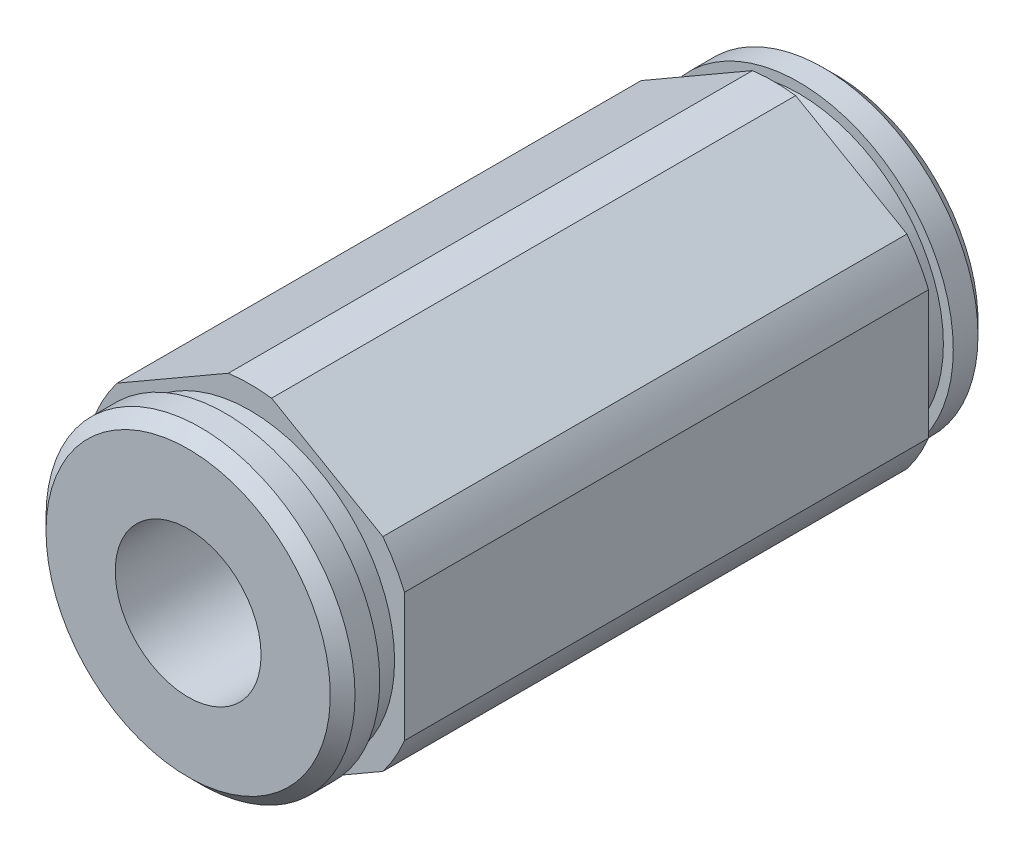
SolidWorks part; units mm, degrees
material "ThunderHex"
ref_plane "Front Plane" through (0, 0, 0) normal (0, 0, 1) x (1, 0, 0)
ref_plane "Top Plane" through (0, 0, 0) normal (0, 1, 0) x (1, 0, 0)
ref_plane "Right Plane" through (0, 0, 0) normal (1, 0, 0) x (0, 0, -1)
ref_plane "End1" through (0, 0, 10.7696) normal (0, 0, 1) x (1, 0, 0)
ref_plane "End2" through (0, 0, -10.7696) normal (0, 0, 1) x (1, 0, 0)
sketch "Sketch1" plane through (0, 0, 0) normal (0, 0, 1) x (1, 0, 0)
  circle A0 centre (0, 0) radius 6.35
  dimension "D1" = 12.7
extrude "Basic Rod" add sketch "Sketch1" along normal up to surface (10.7696 mm away) and the other way up to surface (10.7696 mm away) up to plane "End1" other way up to plane "End2"
ref_axis "Center Axis" through (0, 0, -38.2778) along (0, 0, 1)
sketch "Sketch8" plane through (0, 0, 0) normal (0, 0, 1) x (1, 0, 0)
  line L0 (-5.4616, 4.1791) -> (-6.35, 3.6662) construction
  line L1 (-0.8884, 6.8194) -> (-5.4616, 4.1791)
  line L2 (-6.35, 2.6403) -> (-6.35, -2.6403)
  line L3 (-5.4616, -4.1791) -> (-0.8884, -6.8194)
  line L4 (0.8884, -6.8194) -> (5.4616, -4.1791)
  line L5 (6.35, -2.6403) -> (6.35, 2.6403)
  line L6 (5.4616, 4.1791) -> (0.8884, 6.8194)
  line L7 (-6.35, 3.6662) -> (-6.35, 2.6403) construction
  line L8 (0, 7.3323) -> (-0.8884, 6.8194) construction
  line L9 (0.8884, 6.8194) -> (0, 7.3323) construction
  line L10 (6.35, 3.6662) -> (5.4616, 4.1791) construction
  line L11 (6.35, 2.6403) -> (6.35, 3.6662) construction
  line L12 (6.35, -3.6662) -> (6.35, -2.6403) construction
  line L13 (5.4616, -4.1791) -> (6.35, -3.6662) construction
  line L14 (0, -7.3323) -> (0.8884, -6.8194) construction
  line L15 (-0.8884, -6.8194) -> (0, -7.3323) construction
  line L16 (-6.35, -3.6662) -> (-5.4616, -4.1791) construction
  line L17 (-6.35, -2.6403) -> (-6.35, -3.6662) construction
  circle A0 centre (0, 0) radius 6.35 construction
  arc A1 (-6.35, -2.6403) -> (-5.4616, -4.1791) centre (0, 0) ccw
  circle A2 centre (0, 0) radius 6.35 construction
  arc A3 (-6.35, 2.6403) -> (-6.35, -2.6403) centre (0, 0) ccw construction
  arc A4 (-0.8884, 6.8194) -> (-5.4616, 4.1791) centre (0, 0) ccw construction
  arc A5 (-5.4616, 4.1791) -> (-6.35, 2.6403) centre (0, 0) ccw
  arc A6 (5.4616, 4.1791) -> (0.8884, 6.8194) centre (0, 0) ccw construction
  arc A7 (0.8884, 6.8194) -> (-0.8884, 6.8194) centre (0, 0) ccw
  arc A8 (6.35, -2.6403) -> (6.35, 2.6403) centre (0, 0) ccw construction
  arc A9 (6.35, 2.6403) -> (5.4616, 4.1791) centre (0, 0) ccw
  arc A10 (0.8884, -6.8194) -> (5.4616, -4.1791) centre (0, 0) ccw construction
  arc A11 (5.4616, -4.1791) -> (6.35, -2.6403) centre (0, 0) ccw
  arc A12 (-5.4616, -4.1791) -> (-0.8884, -6.8194) centre (0, 0) ccw construction
  arc A13 (-0.8884, -6.8194) -> (0.8884, -6.8194) centre (0, 0) ccw
  dimension "D1" = 13.7541
extrude "THex" add sketch "Sketch8" along normal mid plane 21.5392
sketch "Sketch5" plane through (0, 0, 0) normal (0, 0, 1) x (1, 0, 0)
  line L1 (-3.6662, 6.35) -> (-7.3323, 0)
  line L2 (-7.3323, 0) -> (-3.6662, -6.35)
  line L3 (-3.6662, -6.35) -> (3.6662, -6.35)
  line L4 (3.6662, -6.35) -> (7.3323, 0)
  line L5 (7.3323, 0) -> (3.6662, 6.35)
  line L6 (3.6662, 6.35) -> (-3.6662, 6.35)
  circle A0 centre (0, 0) radius 6.35 construction
  circle A2 centre (0, 0) radius 6.35 construction
extrude "Hex" [suppressed] add sketch "Sketch5" along normal mid plane 21.5392
sketch "Sketch7" plane through (0, 0, 0) normal (1, 0, 0) x (0, 0, -1)
  line L0 (0, 0) -> (-50000, 0) construction
  line L1 (-10.7696, 5.9436) -> (-11.7856, 5.9436)
  line L2 (-11.7856, 5.9436) -> (-11.7856, 6.35)
  line L3 (-11.7856, 6.35) -> (-12.8016, 6.35)
  line L4 (-13.3096, 5.842) -> (-13.3096, 0)
  line L5 (-13.3096, 0) -> (-10.7696, 0)
  line L6 (-10.7696, 0) -> (-10.7696, 5.9436)
  line L7 (-12.8016, 6.35) -> (-13.3096, 5.842)
  line L8 (38.2778, 0) -> (-38.2778, 0) construction
  line L9 (-10.7696, 5.2388) -> (-10.7696, -5.2388) construction
  point P7 (-13.3096, 6.35)
  dimension "D1" = 12.7
  dimension "D4" = 1.016
  dimension "D2" = 0.4064
  dimension "D3" = 2.54
revolve "1stSnapRing" add sketch "Sketch7" angle 360 about axis through (0, 0, -38.2778) along (0, 0, 1)
mirror "2ndSnapRing" about plane through (0, 0, 0) normal (0, 0, 1) of "1stSnapRing"
sketch "Sketch2" plane through (0, 0, 0) normal (0, 0, 1) x (1, 0, 0)
  circle A0 centre (0, 0) radius 2.9972
  dimension "D1" = 5.9944
extrude "Internal Cut" cut sketch "Sketch2" against normal through all both and the other way through all
equation "\"Unit Measure\"= \"Length\"'in"
equation "\"D1@Sketch1\"=\"OD\""
equation "\"D1\"= \"Length\""
equation "\"D1@Sketch2\"=\"ID\""
equation "\"Internal Cut\"= IIF ( \"ID\" = 0 ,  suppressed  ,  unsuppressed  ) "
equation "\"D1@Hex\" = \"Length\""
equation "\"Hex\" = IIF ( \"SelectionType\" = 1 , \"suppressed\" , iif ( \"SelectionType\" = 2 , \"suppressed\" , \"unsuppressed\" ) )"
equation "\"OutsideDiameter\"= \"OD\"'in"
equation "\"ThunderHexDia\"= iif ( \"OD\" < .36 , \"OD\" * 1.1 , iif ( \"OD\" < .40 , .4035 , iif ( \"OD\" < .52 , .5415 , \"OD\" * 1.1 ) ) )"
equation "\"D1@Sketch7\"=\"Thickness\""
equation "\"SRDia\"= iif ( \"OD\" = .5 , ( \"OD\" - .468 ) / 2 , iif ( \"OD\" = .375 , ( \"OD\" - .352 ) / 2 , .050 ) )"
equation "\"D2@Sketch7\"= \"SnapRingDepth\""
equation "\"1stSnapRing\"= iif ( \"SnapRingCount\" > 0 , \"unsuppressed\" , \"suppressed\" )"
equation "\"2ndSnapRing\"= iif ( \"SnapRingCount\" = 2 , \"unsuppressed\" , \"suppressed\" )"
equation "\"D1@End1\" = \"Length\" / 2"
equation "\"D1@End2\" = \"Length\""
equation "\"D1@Sketch8\"=\"ThunderHexDia\""
equation "\"D1@THex\" = \"Length\""
equation "\"THex\"= IIF ( \"SelectionType\" = 0 ,  suppressed  , iif ( \"SelectionType\" = 2 ,  suppressed  ,  unsuppressed  )  ) "
